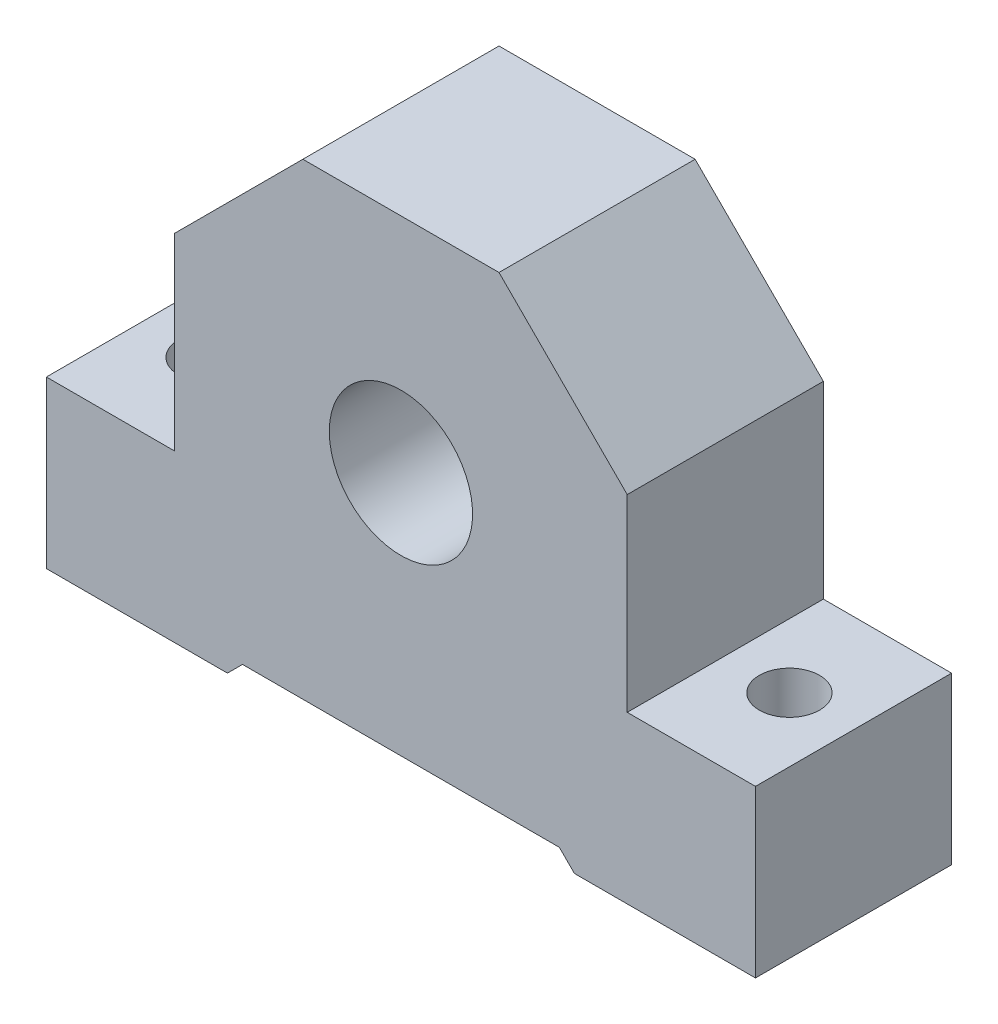
SolidWorks part; units mm, degrees
ref_plane "Płaszczyzna przednia" through (0, 0, 0) normal (0, 0, 1) x (1, 0, 0)
ref_plane "Płaszczyzna górna" through (0, 0, 0) normal (0, 1, 0) x (1, 0, 0)
ref_plane "Płaszczyzna prawa" through (0, 0, 0) normal (1, 0, 0) x (0, 0, -1)
sketch "Szkic1" plane through (0, 0, 0) normal (0, 0, 1) x (1, 0, 0)
  line L0 (-47, 11) -> (-30, 11)
  line L2 (47, -11) -> (47, 11)
  line L4 (-47, -11) -> (-47, 11)
  line L5 (47, -11) -> (-47, 11) construction
  line L6 (47, 11) -> (-47, -11) construction
  line L7 (-30, 11) -> (-30, 36)
  line L8 (-30, 36) -> (-13, 53)
  line L9 (-13, 53) -> (13, 53)
  line L10 (13, 53) -> (30, 36)
  line L11 (30, 36) -> (30, 11)
  line L12 (30, 11) -> (47, 11)
  line L13 (-47, -11) -> (-23, -11)
  line L14 (-23, -11) -> (-21, -9)
  line L15 (-21, -9) -> (21, -9)
  line L16 (21, -9) -> (23, -11)
  line L17 (23, -11) -> (47, -11)
  point P0 (0, 0)
  point P18 (35, -11)
  dimension "D1" = 94
  dimension "D2" = 26
  dimension "D3" = 26
  dimension "D4" = 135
  dimension "D5" = 135
  dimension "D6" = 17
  dimension "D7" = 26
  dimension "D8" = 2
  dimension "D9" = 135
  dimension "D10" = 135
  dimension "D11" = 64
  dimension "D12" = 22
  dimension "D13" = 60
  dimension "D14" = 17
  dimension "D15" = 17
extrude "Dodanie-wyciągnięcie1" add sketch "Szkic1" along normal blind 26
sketch "Szkic3" plane through (0, 0, 0) normal (0, 0, -1) x (-1, 0, 0)
  line L0 (-13, 53) -> (13, 53) construction
  circle A0 centre (0, 23.5) radius 9.5
  point P4 (0, 0)
  dimension "D1" = 29.5
  dimension "D2" = 19
extrude "Wytnij-wyciągnięcie1" cut sketch "Szkic3" against normal blind 26
sketch "Szkic4" plane through (0, 11, 0) normal (0, 1, 0) x (1, 0, 0)
  line L0 (47, -26) -> (47, 0) construction
  line L1 (47, 0) -> (30, 0) construction
  line L2 (-47, -26) -> (-47, 0) construction
  line L3 (-30, 0) -> (-47, 0) construction
  circle A0 centre (38.5, -13) radius 4
  circle A1 centre (-38.5, -13) radius 4
  point P10 (-47, -13)
  dimension "D1" = 8.5
  dimension "D3" = 8.5
  dimension "D5" = 8
  dimension "D6" = 8
  dimension "D2" = 13
  dimension "D4" = 13
extrude "Wytnij-wyciągnięcie2" cut sketch "Szkic4" against normal blind 22
